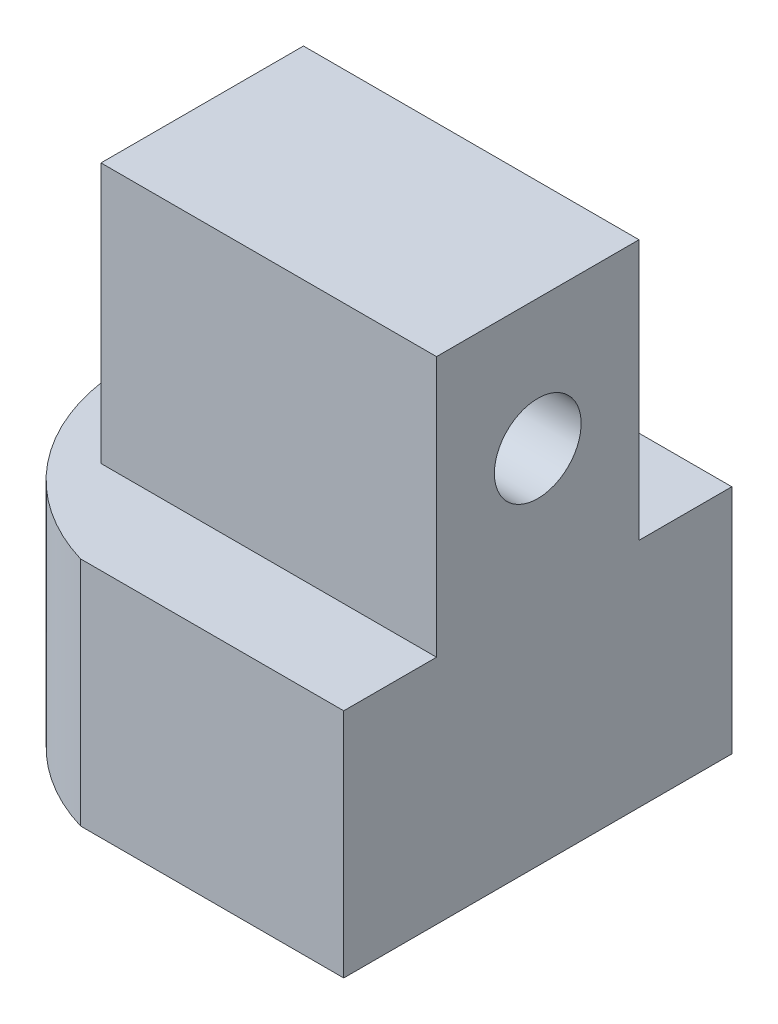
SolidWorks part; units mm, degrees
ref_plane "Спереди" through (0, 0, 0) normal (0, 0, 1) x (1, 0, 0)
ref_plane "Сверху" through (0, 0, 0) normal (0, 1, 0) x (1, 0, 0)
ref_plane "Справа" through (0, 0, 0) normal (1, 0, 0) x (0, 0, -1)
sketch "Sketch1" plane through (0, 0, 0) normal (0, 1, 0) x (1, 0, 0)
  circle A0 centre (0, 0) radius 4
  circle A1 centre (0, 0) radius 7
  dimension "D1" = 8
  dimension "D2" = 14
extrude "Boss-Extrude1" add sketch "Sketch1" along normal blind 6
sketch "Sketch2" plane through (0, 6, 0) normal (0, 1, 0) x (1, 0, 0)
  circle A0 centre (0, 0) radius 7
  circle A1 centre (0, 0) radius 7 construction
extrude "Boss-Extrude2" add sketch "Sketch2" along normal blind 10
sketch "Sketch3" plane through (0, 16, 0) normal (0, 1, 0) x (1, 0, 0)
  line L0 (0, 7) -> (0, -7)
  circle A0 centre (0, 0) radius 7 construction
  arc A1 (0, -7) -> (0, 7) centre (0, 0) cw
extrude "Cut-Extrude1" cut sketch "Sketch3" against normal blind 8
sketch "Sketch4" plane through (0, 0, 0) normal (-1, 0, 0) x (0, 0, 1)
  line L0 (0, 8) -> (0, 16) construction
  line L1 (7, 8) -> (-7, 8) construction
  line L2 (7, 16) -> (-7, 16) construction
  line L4 (2.15, 15.3) -> (-2.15, 15.3)
  line L5 (2.15, 15.3) -> (2.15, 9)
  line L6 (2.15, 9) -> (-2.15, 9)
  line L7 (-2.15, 15.3) -> (-2.15, 9)
  line L8 (2.15, 15.3) -> (-2.15, 9) construction
  line L9 (2.15, 9) -> (-2.15, 15.3) construction
  point P6 (0, 12.15)
  point P11 (0, 0)
  point P12 (0, 0)
  dimension "D1" = 6.3
  dimension "D2" = 4.3
  dimension "D3" = 1
extrude "Cut-Extrude2" cut sketch "Sketch4" against normal blind 6
sketch "Sketch5" plane through (0, 16, 0) normal (0, 1, 0) x (1, 0, 0)
  line L0 (0, 4) -> (5.7446, 4)
  line L1 (0, -7) -> (0, 7) construction
  line L2 (0, -4) -> (5.7446, -4)
  line L3 (0, 4) -> (0, -4)
  arc A0 (0, -7) -> (0, 7) centre (0, 0) ccw construction
  arc A1 (5.7446, 4) -> (5.7446, -4) centre (0, 0) cw
  dimension "D1" = 8
  dimension "D2" = 4
extrude "Cut-Extrude3" cut sketch "Sketch5" against normal up to surface (8 mm away) flip side to cut up to face at (-3.5, 8, 0)
sketch "Sketch7" plane through (0, 8, 0) normal (0, 1, 0) x (1, 0, 0)
  line L0 (0, 7) -> (0, -7) construction
  line L1 (2, 6.7082) -> (2, 11.7082)
  line L2 (2, 11.7082) -> (-2, 11.7082)
  line L3 (-2, 11.7082) -> (-2, 6.7082)
  line L4 (2, -6.7082) -> (2, -11.7082)
  line L5 (2, -11.7082) -> (-2, -11.7082)
  line L6 (-2, -11.7082) -> (-2, -6.7082)
  arc A0 (5.7446, 4) -> (5.7446, -4) centre (0, 0) ccw construction
  arc A1 (2, 6.7082) -> (-2, 6.7082) centre (0, 0) ccw
  arc A2 (2, -6.7082) -> (-2, -6.7082) centre (0, 0) cw
  point P16 (0, 0)
  dimension "D1" = 4
  dimension "D2" = 5
extrude "Boss-Extrude3" add sketch "Sketch7" against normal up to surface (8 mm away) up to face at (0, 0, 7)
sketch "Sketch9" plane through (0, 16, 0) normal (0, 1, 0) x (1, 0, 0)
  line L0 (0, -4) -> (0, 4) construction
  circle A0 centre (0, 0) radius 7
  arc A1 (-2, 6.7082) -> (-2, -6.7082) centre (0, 0) ccw construction
extrude "Cut-Extrude6" cut sketch "Sketch9" against normal up to surface (8 mm away) up to face at (0.5791, 8, 0)
sketch "Sketch10" plane through (0, 8, 0) normal (0, 1, 0) x (1, 0, 0)
  line L1 (-4.5, -3.5) -> (4.5, -3.5)
  line L2 (-4.5, -3.5) -> (-4.5, 3.5)
  line L3 (-4.5, 3.5) -> (4.5, 3.5)
  line L4 (4.5, -3.5) -> (4.5, 3.5)
  line L5 (-4.5, -3.5) -> (4.5, 3.5) construction
  line L6 (-4.5, 3.5) -> (4.5, -3.5) construction
  point P0 (0, 0)
  dimension "D1" = 7
  dimension "D2" = 9
extrude "Boss-Extrude5" add sketch "Sketch10" along normal blind 9
sketch "Sketch11" plane through (-4.5, 0, 0) normal (-1, 0, 0) x (0, 0, 1)
  line L0 (0, 17) -> (0, 8) construction
  line L1 (-3.5, 17) -> (3.5, 17) construction
  line L2 (-3.5, 8) -> (3.5, 8) construction
  line L4 (2.15, 9.35) -> (-2.15, 9.35)
  line L5 (2.15, 9.35) -> (2.15, 15.65)
  line L6 (2.15, 15.65) -> (-2.15, 15.65)
  line L7 (-2.15, 9.35) -> (-2.15, 15.65)
  line L8 (2.15, 9.35) -> (-2.15, 15.65) construction
  line L9 (2.15, 15.65) -> (-2.15, 9.35) construction
  point P6 (0, 12.5)
  dimension "D1" = 4.3
  dimension "D2" = 6.3
extrude "Cut-Extrude7" cut sketch "Sketch11" against normal blind 6
sketch "Sketch13" plane through (0, 8, 0) normal (0, 1, 0) x (1, 0, 0)
  line L0 (2, -6.7082) -> (7.1, -6.7082)
  line L1 (7.1, -6.7082) -> (7.1, 6.7082)
  line L2 (7.1, 6.7082) -> (2, 6.7082)
  arc A0 (2, -6.7082) -> (2, 6.7082) centre (0, 0) ccw construction
  arc A1 (2, 6.7082) -> (2, -6.7082) centre (0, 0) cw
  point P3 (7.1, 0)
  point P10 (7, 0)
  dimension "D1" = 0.1
extrude "Boss-Extrude6" add sketch "Sketch13" against normal up to surface (8 mm away) up to face at (0, 0, 0)
sketch "Sketch14" plane through (4.5, 0, 0) normal (1, 0, 0) x (0, 0, -1)
  line L0 (0, 17) -> (0, 8) construction
  line L1 (-3.5, 17) -> (3.5, 17) construction
  line L2 (-3.5, 8) -> (3.5, 8) construction
  line L4 (-3.5, 8) -> (3.5, 8)
  line L5 (-3.5, 8) -> (-3.5, 17)
  line L6 (-3.5, 17) -> (3.5, 17)
  line L7 (3.5, 8) -> (3.5, 17)
  line L8 (-3.5, 8) -> (3.5, 17) construction
  line L9 (-3.5, 17) -> (3.5, 8) construction
  point P6 (0, 12.5)
extrude "Boss-Extrude7" add sketch "Sketch14" along normal up to surface (2.6 mm away) up to face at (7.1, 4, 0)
sketch "Sketch15" plane through (0, 8, 0) normal (0, 1, 0) x (1, 0, 0)
  line L0 (2, 6.7082) -> (-2, 6.7082)
  line L1 (2, -6.7082) -> (-2, -6.7082)
  line L2 (-2, -6.7082) -> (-2, -11.7082)
  line L3 (-2, -11.7082) -> (2, -11.7082)
  line L4 (2, -11.7082) -> (2, -6.7082)
  line L5 (2, 6.7082) -> (2, 11.7082)
  line L6 (2, 11.7082) -> (-2, 11.7082)
  line L7 (-2, 11.7082) -> (-2, 6.7082)
extrude "Cut-Extrude10" cut sketch "Sketch15" against normal through all
sketch "Sketch16" plane through (1.5, 0, 0) normal (-1, 0, 0) x (0, 0, 1)
  line L0 (0, 15.65) -> (0, 9.35) construction
  line L1 (2.15, 15.65) -> (-2.15, 15.65) construction
  line L2 (-2.15, 9.35) -> (2.15, 9.35) construction
  circle A0 centre (0, 12.5) radius 1.5
  dimension "D1" = 3
extrude "Cut-Extrude11" cut sketch "Sketch16" against normal through all
